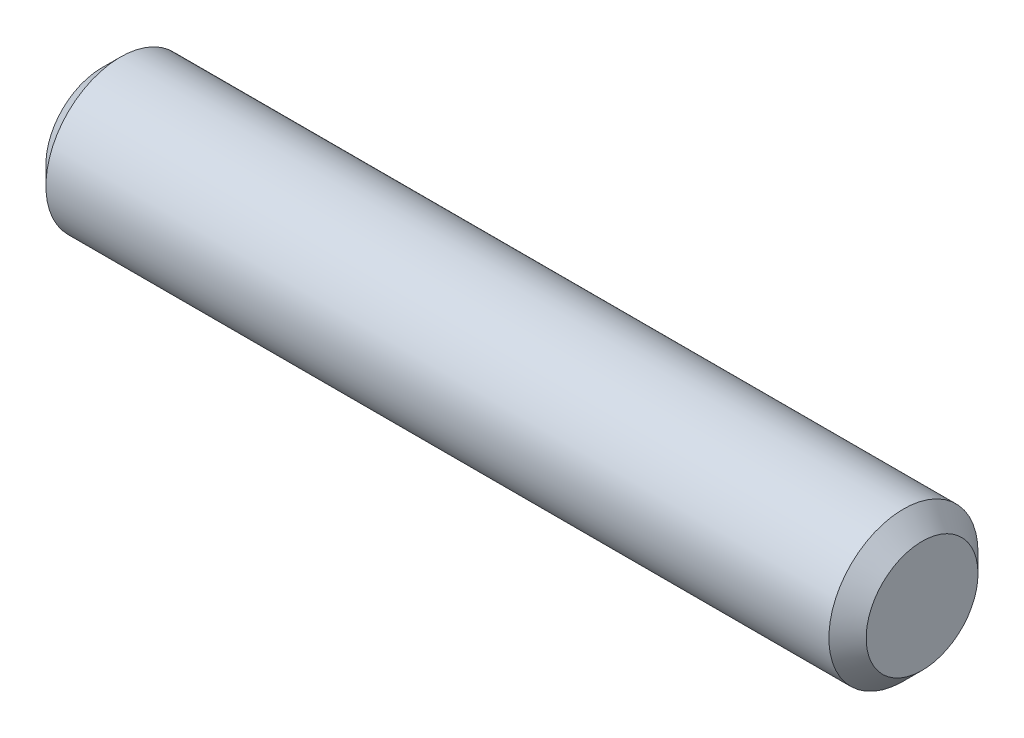
SolidWorks part; units mm, degrees
ref_plane "Front Plane" through (0, 0, 0) normal (0, 0, 1) x (1, 0, 0)
ref_plane "Top Plane" through (0, 0, 0) normal (0, 1, 0) x (1, 0, 0)
ref_plane "Right Plane" through (0, 0, 0) normal (1, 0, 0) x (0, 0, -1)
sketch "Sketch1" plane through (0, 0, 0) normal (1, 0, 0) x (0, 0, -1)
  circle A0 centre (0, 0) radius 2
  dimension "D1" = 4
extrude "Boss-Extrude1" add sketch "Sketch1" along normal mid plane 22
chamfer "Chamfer1" distance 0.5 angle 45 2 edges at (11, 0, -2) (-11, 0, -2)
